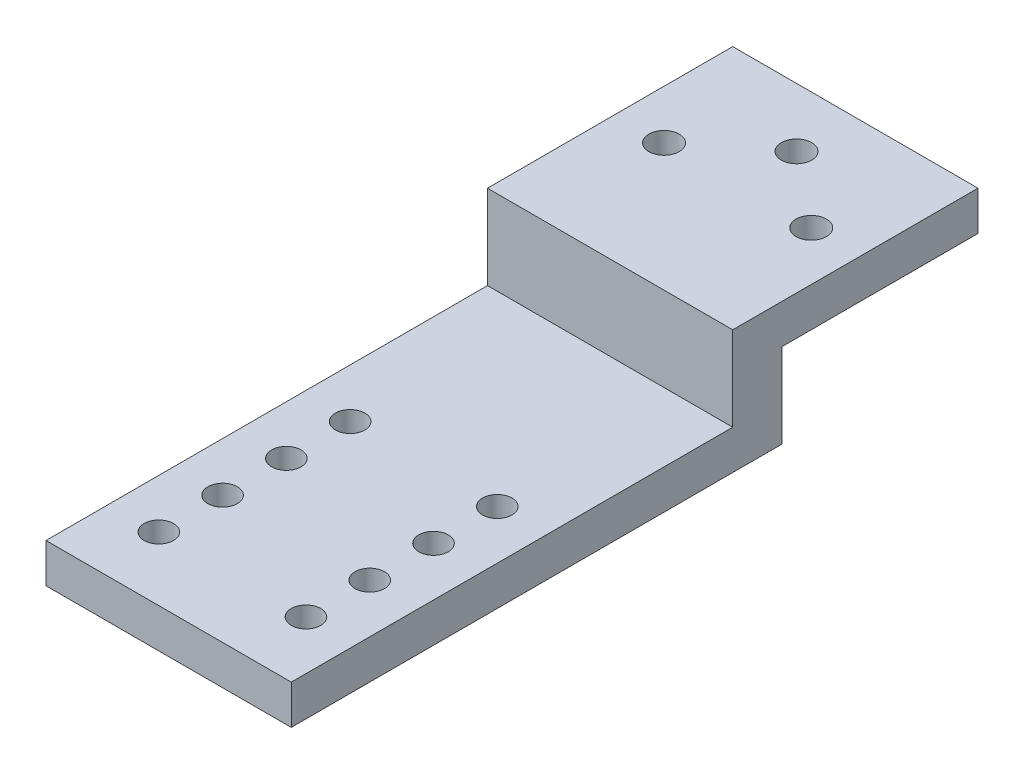
SolidWorks part; units mm, degrees
ref_plane "Спереди" through (0, 0, 0) normal (0, 0, 1) x (1, 0, 0)
ref_plane "Сверху" through (0, 0, 0) normal (0, 1, 0) x (1, 0, 0)
ref_plane "Справа" through (0, 0, 0) normal (1, 0, 0) x (0, 0, -1)
sketch "Эскиз1" plane through (0, 0, 0) normal (0, 1, 0) x (1, 0, 0)
  line L0 (-12.5, 48.8522) -> (-12.5, -21.1478)
  line L1 (-12.5, -21.1478) -> (12.5, -21.1478)
  line L2 (12.5, -21.1478) -> (12.5, 48.8522)
  line L3 (-9, -14.6478) -> (-12.5, -14.6478) construction
  line L4 (9, -14.6478) -> (12.5, -14.6478) construction
  line L5 (-6, -14.6478) -> (6, -14.6478) construction
  line L6 (7.5, -16.1478) -> (7.5, -21.1478) construction
  line L7 (7.5, -13.1478) -> (7.5, -9.6478) construction
  line L8 (-12.5, 48.8522) -> (12.5, 48.8522)
  line L9 (-5.95, 36.8522) -> (5.95, 36.8522) construction
  circle A0 centre (-7.5, 36.8522) radius 1.55
  circle A1 centre (7.5, 36.8522) radius 1.55
  circle A2 centre (-7.5, -14.6478) radius 1.5
  circle A3 centre (7.5, -14.6478) radius 1.5
  circle A4 centre (-7.5, -8.1478) radius 1.5
  circle A5 centre (7.5, -8.1478) radius 1.5
  circle A6 centre (-7.5, -1.6478) radius 1.5
  circle A7 centre (7.5, -1.6478) radius 1.5
  circle A8 centre (-7.5, 4.8522) radius 1.5
  circle A9 centre (7.5, 4.8522) radius 1.5
  circle A10 centre (0, 42.8522) radius 1.55
  point P6 (0, -21.1478)
  point P38 (0, 42.0054)
  point P46 (0, 15.8522)
  dimension "D1" = 25
  dimension "D3" = 3.1
  dimension "D4" = 3
  dimension "D2" = 70
  dimension "D5" = 12
  dimension "D6" = 5
  dimension "D8" = 3.5
  dimension "D10" = 12
  dimension "D9" = 6
  dimension "D7" = 4
extrude "Бобышка-Вытянуть1" add sketch "Эскиз1" along normal blind 4
sketch "Эскиз2" plane through (0, 4, 0) normal (0, 1, 0) x (1, 0, 0)
  line L0 (12.5, -21.1478) -> (12.5, 48.8522) construction
  line L1 (-12.5, 48.8522) -> (12.5, 48.8522)
  line L2 (-12.5, 48.8522) -> (-12.5, 23.8522)
  line L3 (-12.5, 23.8522) -> (12.5, 23.8522)
  line L4 (12.5, 48.8522) -> (12.5, 23.8522)
  circle A0 centre (0, 42.8522) radius 1.55
  circle A1 centre (7.5, 36.8522) radius 1.55
  circle A2 centre (-7.5, 36.8522) radius 1.55
  dimension "D1" = 25
extrude "Бобышка-Вытянуть2" add sketch "Эскиз2" along normal blind 8.6
sketch "Эскиз3" plane through (0, 0, 0) normal (0, -1, 0) x (1, 0, 0)
  line L0 (12.5, 21.1478) -> (12.5, -48.8522) construction
  line L1 (-12.5, -48.8522) -> (12.5, -48.8522)
  line L2 (-12.5, -48.8522) -> (-12.5, -28.8522)
  line L3 (-12.5, -28.8522) -> (12.5, -28.8522)
  line L4 (12.5, -48.8522) -> (12.5, -28.8522)
  circle A0 centre (-7.5, -36.8522) radius 1.55
  circle A1 centre (7.5, -36.8522) radius 1.55
  circle A2 centre (0, -42.8522) radius 1.55
  dimension "D1" = 20
extrude "Вырез-Вытянуть1" cut sketch "Эскиз3" against normal blind 8.6
